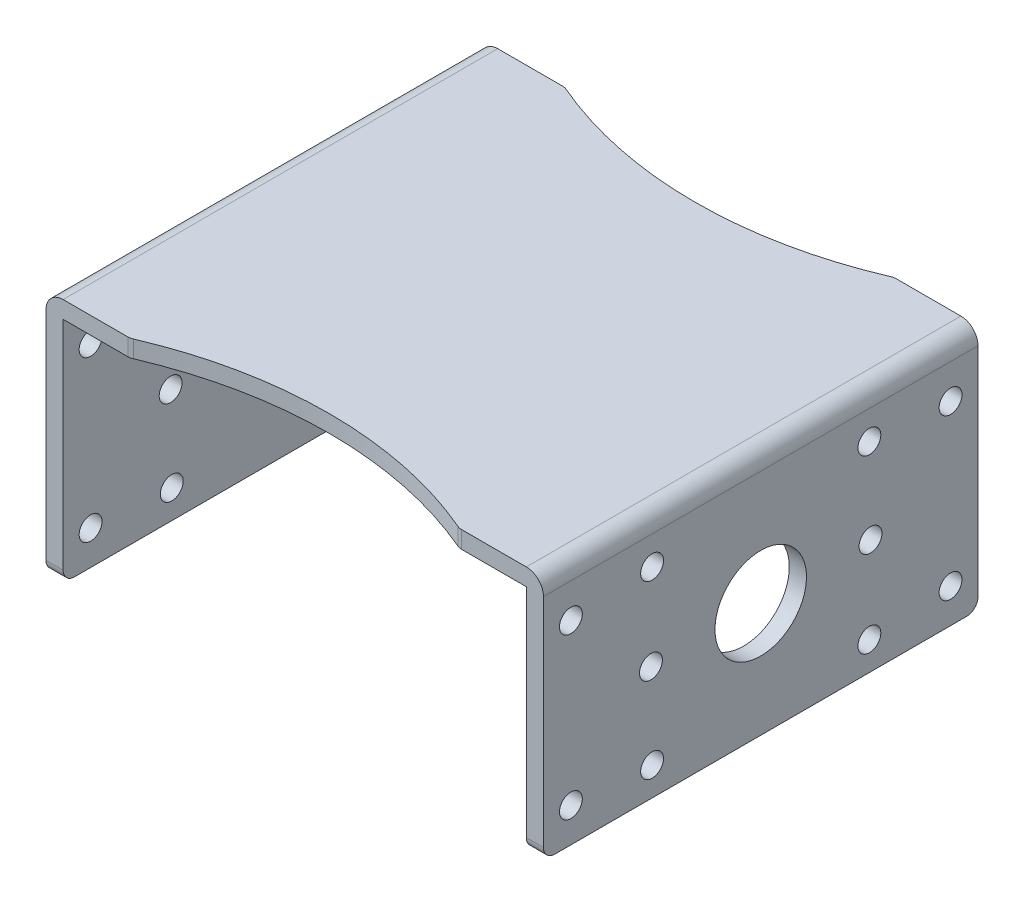
SolidWorks part; units mm, degrees
ref_plane "前视基准面" through (0, 0, 0) normal (0, 0, 1) x (1, 0, 0)
ref_plane "上视基准面" through (0, 0, 0) normal (0, 1, 0) x (1, 0, 0)
ref_plane "右视基准面" through (0, 0, 0) normal (1, 0, 0) x (0, 0, -1)
ref_plane "基准面1" through (0, -20, 0) normal (0, -1, 0) x (1, 0, 0)
sketch "草图1" plane through (0, -20, 0) normal (0, -1, 0) x (1, 0, 0)
  line L0 (21.75, 19) -> (-21.75, 19)
  line L1 (-21.75, 19) -> (-21.75, -19)
  line L2 (-21.75, -19) -> (21.75, -19)
  line L3 (21.75, -19) -> (21.75, 19)
extrude "凸台-拉伸1" add sketch "草图1" against normal blind 21.5
sketch "草图2" plane through (0, 0, 19) normal (0, 0, 1) x (1, 0, 0)
  line L0 (-20.25, -20) -> (20.25, -20)
  line L1 (20.25, -20) -> (20.25, 0)
  line L2 (20.25, 0) -> (-20.25, 0)
  line L3 (-20.25, 0) -> (-20.25, -20)
extrude "切除-拉伸1" cut sketch "草图2" against normal through all
sketch "草图3" plane through (0, 1.5, 0) normal (0, 1, 0) x (-1, 0, 0)
  line L0 (14.3875, 19) -> (-14.3875, 19)
  arc A0 (-14.3875, 19) -> (14.3875, 19) centre (0, 52) ccw
extrude "切除-拉伸2" cut sketch "草图3" against normal through all
sketch "草图4" plane through (0, 1.5, 0) normal (0, 1, 0) x (-1, 0, 0)
  line L0 (-14.3875, -19) -> (14.3875, -19)
  arc A0 (14.3875, -19) -> (-14.3875, -19) centre (0, -52) ccw
extrude "切除-拉伸3" cut sketch "草图4" against normal through all
hole_wizard "Ø8.0 (8) 直径孔1" positions "草图6" profile "草图5" hole size "Ø8.0" standard "ANSI Metric"
sketch "草图6" plane through (20.25, 0, 0) normal (-1, 0, 0) x (0, 0, 1)
  point P0 (0, -10)
sketch "草图5" plane through (20.25, -10, 0) normal (0, 1, 0) x (0, 0, 1)
  line L0 (0, 0) -> (0, 1.5)
  line L1 (0, 1.5) -> (4, 1.5)
  line L2 (4, 1.5) -> (4, 0)
  line L5 (4, 0) -> (0, 0)
  line L11 (0, -6.35) -> (0, 107.95) construction
  dimension "通孔孔直径" = 8
  dimension "通孔孔深度" = 1.5
hole_wizard "Ø2.0 (2) 直径孔1" positions "草图8" profile "草图7" hole size "Ø2.0" standard "ANSI Metric"
sketch "草图8" plane through (20.25, 0, 0) normal (-1, 0, 0) x (0, 0, 1)
  point P0 (16.6, -3)
  point P1 (16.6, -17)
  point P2 (9.5, -17.5)
  point P3 (9.6, -10)
  point P4 (9.5, -2.5)
  point P5 (-9.5, -2.5)
  point P6 (-16.6, -3)
  point P7 (-16.6, -17)
  point P8 (-9.5, -17.5)
  point P9 (-9.6, -10)
sketch "草图7" plane through (20.25, -3, 16.6) normal (0, 1, 0) x (0, 0, 1)
  line L0 (0, 0) -> (0, 1.5)
  line L1 (0, 1.5) -> (1, 1.5)
  line L2 (1, 1.5) -> (1, 0)
  line L5 (1, 0) -> (0, 0)
  line L11 (0, -6.35) -> (0, 107.95) construction
  dimension "通孔孔直径" = 2
  dimension "通孔孔深度" = 1.5
hole_wizard "Ø8.0 (8) 直径孔2" positions "草图10" profile "草图9" hole size "Ø8.0" standard "ANSI Metric"
sketch "草图10" plane through (-20.25, 0, 0) normal (1, 0, 0) x (0, 0, -1)
  point P0 (0, -10)
sketch "草图9" plane through (-20.25, -10, 0) normal (0, 1, 0) x (0, 0, -1)
  line L0 (0, 0) -> (0, 1.5)
  line L1 (0, 1.5) -> (4, 1.5)
  line L2 (4, 1.5) -> (4, 0)
  line L5 (4, 0) -> (0, 0)
  line L11 (0, -6.35) -> (0, 107.95) construction
  dimension "通孔孔直径" = 8
  dimension "通孔孔深度" = 1.5
hole_wizard "Ø2.0 (2) 直径孔2" positions "草图12" profile "草图11" hole size "Ø2.0" standard "ANSI Metric"
sketch "草图12" plane through (-20.25, 0, 0) normal (1, 0, 0) x (0, 0, -1)
  point P0 (-16.6, -3)
  point P1 (-16.6, -17)
  point P2 (-9.5, -17.5)
  point P3 (-9.6, -10)
  point P4 (-9.5, -2.5)
  point P5 (9.5, -2.5)
  point P6 (16.6, -3)
  point P7 (16.6, -17)
  point P8 (9.5, -17.5)
  point P9 (9.6, -10)
sketch "草图11" plane through (-20.25, -3, 16.6) normal (0, 1, 0) x (0, 0, -1)
  line L0 (0, 0) -> (0, 1.5)
  line L1 (0, 1.5) -> (1, 1.5)
  line L2 (1, 1.5) -> (1, 0)
  line L5 (1, 0) -> (0, 0)
  line L11 (0, -6.35) -> (0, 107.95) construction
  dimension "通孔孔直径" = 2
  dimension "通孔孔深度" = 1.5
fillet "圆角1" radius 1 8 edges at (14.3875, 0.75, 19) (-14.3875, 0.75, 19) (21, -20, 19) (-14.3875, 0.75, -19) (14.3875, 0.75, -19) (-21, -20, -19) (21, -20, -19) (-21, -20, 19)
fillet "圆角2" radius 1.5 2 edges at (21.75, 1.5, 0) (-21.75, 1.5, 0)
